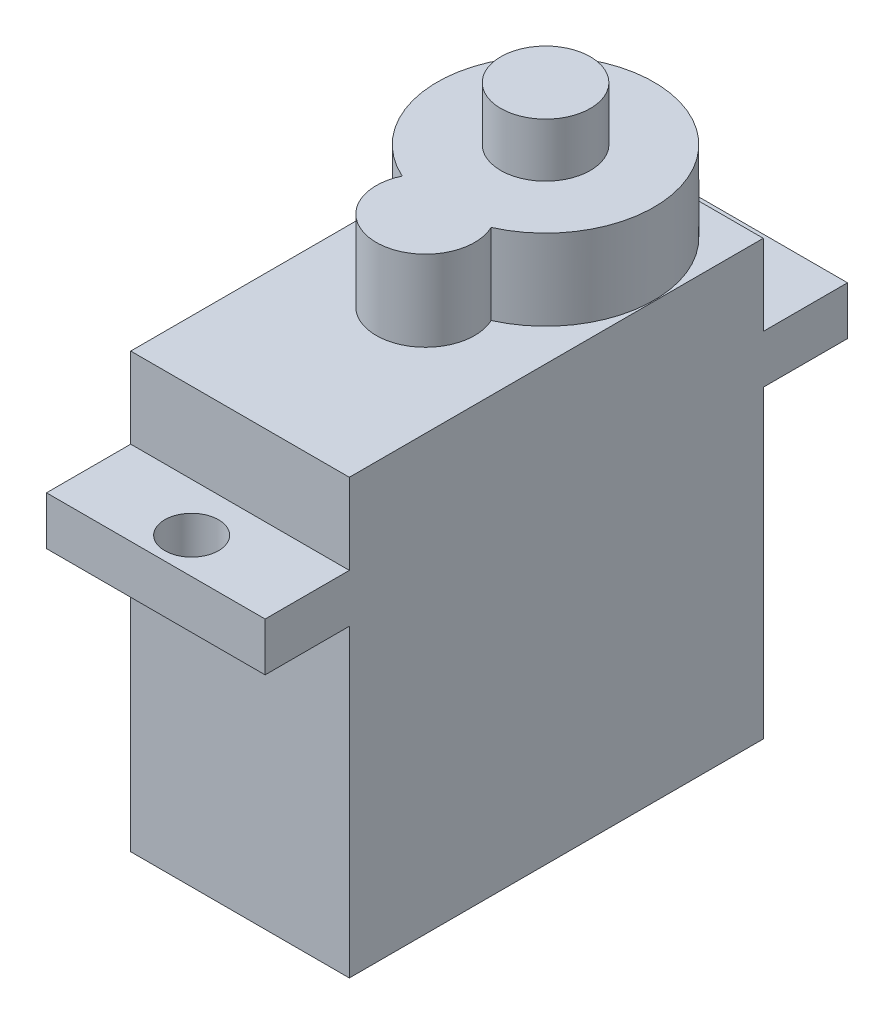
SolidWorks part; units mm, degrees
material "PVC 0.007 Plasticized"
ref_plane "Front Plane" through (0, 0, 0) normal (0, 0, 1) x (1, 0, 0)
ref_plane "Top Plane" through (0, 0, 0) normal (0, 1, 0) x (1, 0, 0)
ref_plane "Right Plane" through (0, 0, 0) normal (1, 0, 0) x (0, 0, -1)
sketch "Sketch1" plane through (0, 0, 0) normal (0, 1, 0) x (1, 0, 0)
  line L1 (-6.1, -11.55) -> (6.1, -11.55)
  line L2 (-6.1, -11.55) -> (-6.1, 11.55)
  line L3 (-6.1, 11.55) -> (6.1, 11.55)
  line L4 (6.1, -11.55) -> (6.1, 11.55)
  line L5 (-6.1, -11.55) -> (6.1, 11.55) construction
  line L6 (-6.1, 11.55) -> (6.1, -11.55) construction
  point P0 (0, 0)
  dimension "D1" = 23.1
  dimension "D2" = 12.2
extrude "Boss-Extrude3" add sketch "Sketch1" along normal blind 24.2
sketch "Sketch5" plane through (0, 0, 11.55) normal (0, 0, 1) x (1, 0, 0)
  line L0 (0, 24.2) -> (0, 19.7) construction
  line L1 (-6.1, 24.2) -> (6.1, 24.2) construction
  line L2 (-6.1, 19.7) -> (6.1, 19.7)
  line L3 (6.1, 24.2) -> (6.1, 0) construction
  line L4 (-6.1, 19.7) -> (-6.1, 17)
  line L5 (-6.1, 24.2) -> (-6.1, 0) construction
  line L6 (-6.1, 17) -> (6.1, 17)
  line L7 (6.1, 17) -> (6.1, 19.7)
  point P10 (0, 19.7)
  dimension "D1" = 4.5
  dimension "D2" = 2.7
extrude "Boss-Extrude4" add sketch "Sketch5" along normal blind 4.7
sketch "Sketch6" plane through (0, 19.7, 0) normal (0, 1, 0) x (1, 0, 0)
  line L0 (6.1, -16.25) -> (-6.1, -16.25) construction
  line L2 (6.1, -16.25) -> (6.1, -11.55) construction
  circle A0 centre (0, -14.25) radius 1.5
  dimension "D1" = 3
  dimension "D2" = 2
  dimension "D3" = 6.1
extrude "Cut-Extrude4" cut sketch "Sketch6" against normal through all both contours A0
mirror "Mirror3" about plane through (0, 0, 0) normal (0, 0, 1) of "Cut-Extrude4", "Boss-Extrude4"
sketch "Sketch7" plane through (0, 24.2, 0) normal (0, 1, 0) x (1, 0, 0)
  line L0 (6.1, 11.55) -> (-6.1, 11.55) construction
  line L1 (6.1, -11.55) -> (6.1, 11.55) construction
  circle A0 centre (0, 5.5) radius 6.05
  circle A1 centre (0, -1.2) radius 2.75
  dimension "D1" = 12.1
  dimension "D3" = 5.5
  dimension "D2" = 1.2
  dimension "D4" = 6.1
  dimension "D5" = 6.1
extrude "Boss-Extrude5" add sketch "Sketch7" along normal blind 4.5 contours A1 A0 | A0 A1 | A0 A1
sketch "Sketch8" plane through (0, 28.7, 0) normal (0, 1, 0) x (1, 0, 0)
  circle A0 centre (0, 5.5) radius 2.5
  dimension "D1" = 5
extrude "Boss-Extrude6" add sketch "Sketch8" along normal blind 3
